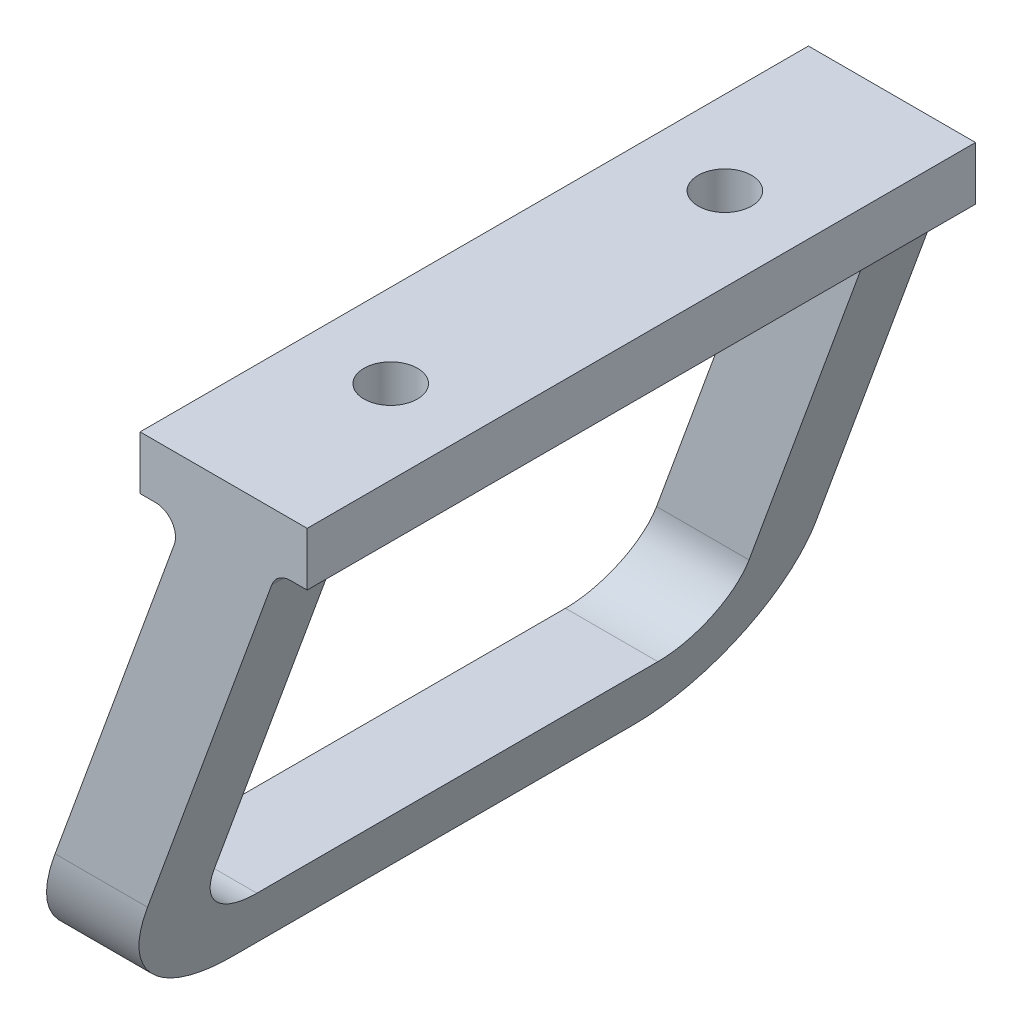
SolidWorks part; units mm, degrees
ref_plane "Front Plane" through (0, 0, 0) normal (0, 0, 1) x (1, 0, 0)
ref_plane "Top Plane" through (0, 0, 0) normal (0, 1, 0) x (1, 0, 0)
ref_plane "Right Plane" through (0, 0, 0) normal (1, 0, 0) x (0, 0, -1)
sketch "Sketch1" plane through (0, 0, 0) normal (0, 0, 1) x (1, 0, 0)
  line L0 (7.2003, -5.9739) -> (-18.6657, -77.0402)
  line L1 (-12.5, 4) -> (12.5, 4)
  line L2 (-12.5, 4) -> (-12.5, -4)
  line L3 (-12.5, -4) -> (-10.2, -4)
  line L4 (12.5, 4) -> (12.5, -4)
  line L5 (-12.5, 4) -> (12.5, -4) construction
  line L6 (-12.5, -4) -> (12.5, 4) construction
  line L7 (-18.6657, -77.0402) -> (-32.5, -77.0402)
  line L8 (-32.5, -77.0402) -> (-7.3809, -8.0261)
  line L9 (10.0194, -4) -> (12.5, -4)
  arc A0 (10.0194, -4) -> (7.2003, -5.9739) centre (10.0194, -7) ccw
  arc A1 (-7.3809, -8.0261) -> (-10.2, -4) centre (-10.2, -7) ccw
  point P0 (0, 0)
  point P8 (-17.2677, -29.8959)
  point P13 (7.9188, -4)
  dimension "D7" = 3
  dimension "D5" = 19.7
  dimension "D1" = 20
  dimension "D2" = 13
  dimension "D3" = 8
  dimension "D4" = 25
  dimension "D6" = 45
extrude "Boss-Extrude1" add sketch "Sketch1" along normal blind 100 contours L8 L7 L0 L3 | L4 L1 L2 L3
sketch "Sketch4" plane through (-12.5, 0, 0) normal (-1, 0, 0) x (0, 0, 1)
  line L0 (50, -77.0402) -> (50, -17.4202) construction
  line L1 (100, -77.0402) -> (0, -77.0402) construction
  line L2 (100, 4) -> (0, 4) construction
  line L3 (20, -67.0402) -> (80, -67.0402)
  line L4 (10, -57.0402) -> (10, -11)
  line L5 (10, -11) -> (90, -11)
  line L6 (90, -57.0402) -> (90, -11)
  line L7 (10, -67.0402) -> (90, -11) construction
  line L8 (10, -11) -> (90, -67.0402) construction
  line L9 (0, -57.0402) -> (0, -77.0402)
  line L10 (100, -77.0402) -> (0, -77.0402)
  line L11 (100, -77.0402) -> (100, -8.0261) construction
  line L12 (100, -77.0402) -> (100, -8.0261)
  arc A0 (80, -67.0402) -> (90, -57.0402) centre (80, -57.0402) ccw
  arc A1 (20, -67.0402) -> (10, -57.0402) centre (20, -57.0402) cw
  arc A2 (80, -77.0402) -> (100, -57.0402) centre (80, -57.0402) ccw
  arc A3 (0, -57.0402) -> (20, -77.0402) centre (20, -57.0402) ccw
  point P4 (50, -39.0201)
  dimension "D4" = 10
  dimension "D6" = 20
  dimension "D1" = 15
  dimension "D2" = 80
  dimension "D3" = 10
extrude "Cut-Extrude1" cut sketch "Sketch4" against normal through all both and the other way through all contours A1 L3 A0 L6 L5 L4 | A2 L10 L12 | A3 L9 L10
sketch "Sketch5" plane through (0, 4, 0) normal (0, 1, 0) x (1, 0, 0)
  line L0 (0, 0) -> (0, -100) construction
  line L1 (-12.5, -100) -> (12.5, -100) construction
  line L2 (0, -50) -> (9.4753, -50) construction
  circle A0 centre (0, -25) radius 4
  circle A1 centre (0, -75) radius 4
  dimension "D1" = 50
  dimension "D2" = 8
extrude "Cut-Extrude2" cut sketch "Sketch5" against normal through all both and the other way through all
